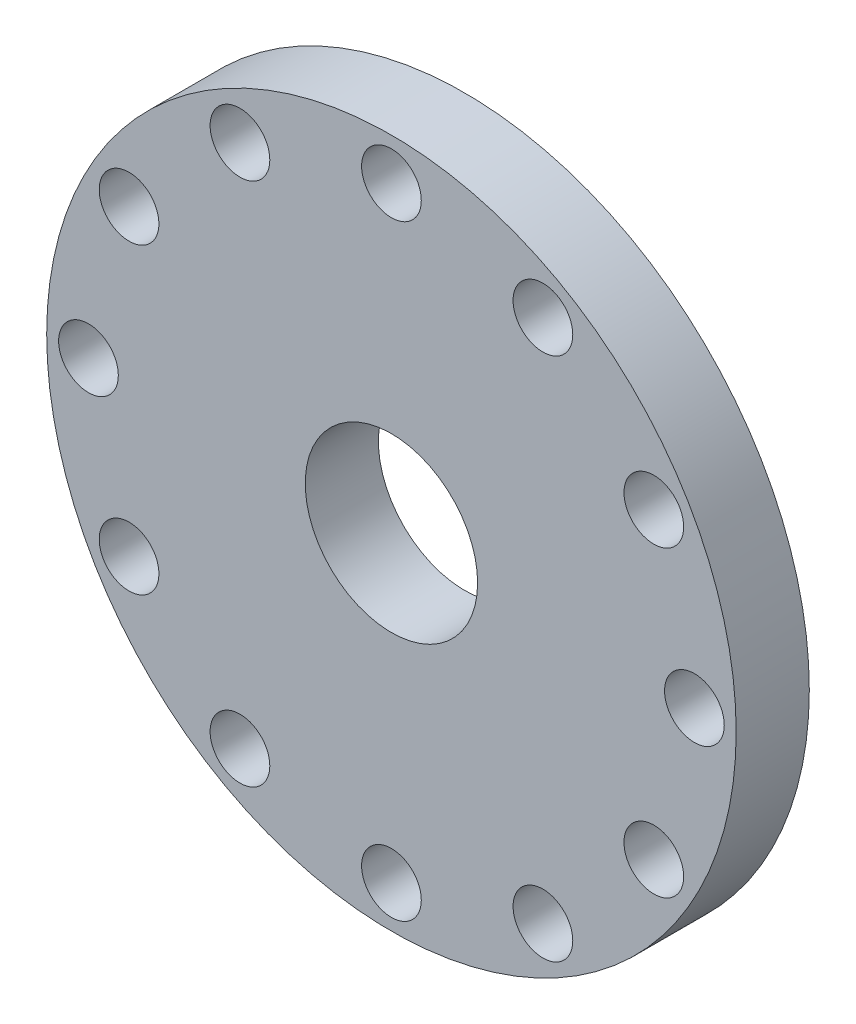
SolidWorks part; units mm, degrees
ref_plane "Front Plane" through (0, 0, 0) normal (0, 0, 1) x (1, 0, 0)
ref_plane "Top Plane" through (0, 0, 0) normal (0, 1, 0) x (1, 0, 0)
ref_plane "Right Plane" through (0, 0, 0) normal (1, 0, 0) x (0, 0, -1)
sketch "Sketch1" plane through (0, 0, 0) normal (0, 0, 1) x (1, 0, 0)
  circle A0 centre (0, 0) radius 330
  circle A1 centre (0, 0) radius 82.5
  dimension "D1" = 660
  dimension "D2" = 165
extrude "Boss-Extrude1" add sketch "Sketch1" along normal blind 70
sketch "Sketch2" plane through (0, 0, 0) normal (0, 0, 1) x (1, 0, 0)
  circle A0 centre (0, 0) radius 290
  circle A1 centre (0, 290) radius 28.575
  circle A2 centre (145, 251.1474) radius 28.575
  circle A3 centre (251.1474, 145) radius 28.575
  circle A4 centre (290, 0) radius 28.575
  circle A5 centre (251.1474, -145) radius 28.575
  circle A6 centre (145, -251.1474) radius 28.575
  circle A7 centre (0, -290) radius 28.575
  circle A8 centre (-145, -251.1474) radius 28.575
  circle A9 centre (-251.1474, -145) radius 28.575
  circle A10 centre (-290, 0) radius 28.575
  circle A11 centre (-251.1474, 145) radius 28.575
  circle A12 centre (-145, 251.1474) radius 28.575
  point P30 (0, 0)
  dimension "D1" = 580
  dimension "D2" = 57.15
  dimension "D3" = 12
extrude "Cut-Extrude1" cut sketch "Sketch2" along normal blind 131 contours A0 A4 | A0 A4 | A0 A6 | A0 A8 | A0 A8 | A5 | A7 | A9 | A10 | A11 | A12 | A1 | A2 | A3
equation "\"2.25inch\"=0.0379964"
